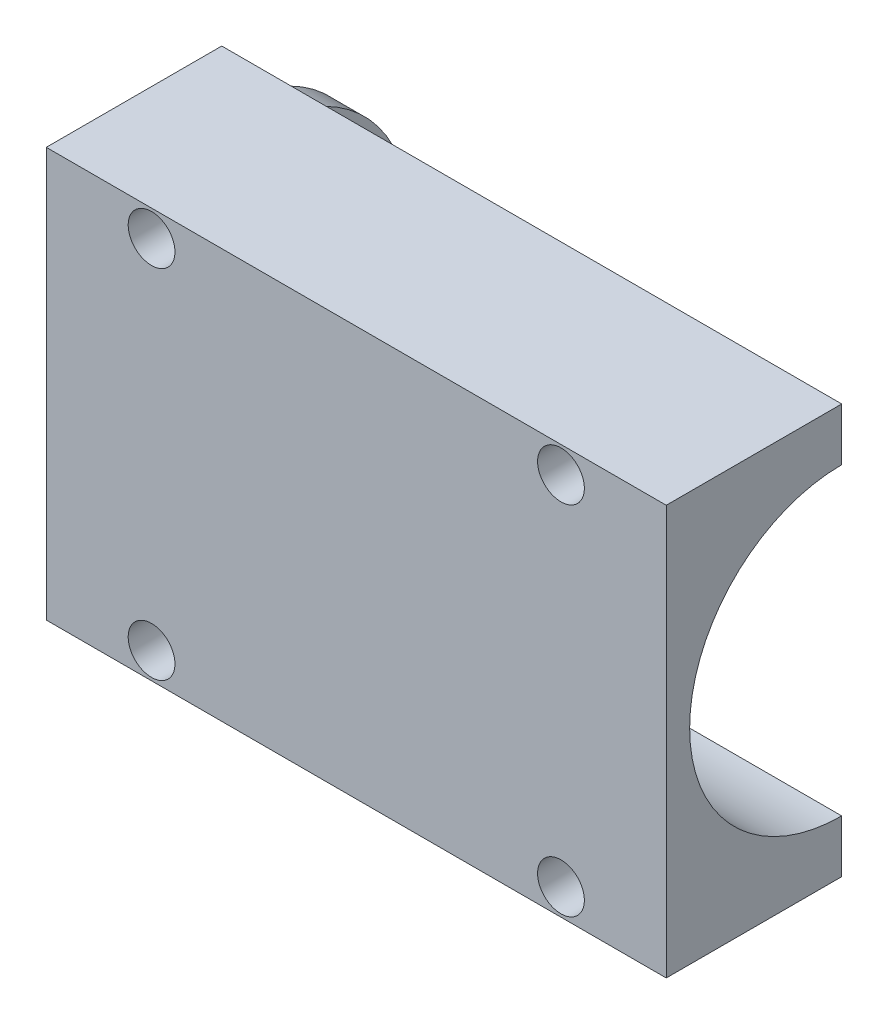
SolidWorks part; units mm, degrees
ref_plane "Front Plane" through (0, 0, 0) normal (0, 0, 1) x (1, 0, 0)
ref_plane "Top Plane" through (0, 0, 0) normal (0, 1, 0) x (1, 0, 0)
ref_plane "Right Plane" through (0, 0, 0) normal (1, 0, 0) x (0, 0, -1)
sketch "Sketch1" plane through (0, 0, 0) normal (0, 0, 1) x (1, 0, 0)
  line L1 (-26.5, -17.5) -> (26.5, -17.5)
  line L2 (-26.5, -17.5) -> (-26.5, 17.5)
  line L3 (-26.5, 17.5) -> (26.5, 17.5)
  line L4 (26.5, -17.5) -> (26.5, 17.5)
  line L5 (-26.5, -17.5) -> (26.5, 17.5) construction
  line L6 (-26.5, 17.5) -> (26.5, -17.5) construction
  point P0 (0, 0)
  point P5 (0, 0)
  dimension "D1" = 53
  dimension "D2" = 35
extrude "Boss-Extrude1" add sketch "Sketch1" along normal blind 15
sketch "Sketch2" plane through (0, 0, 0) normal (1, 0, 0) x (0, 0, -1)
  line L0 (0, -17.5) -> (0, 17.5) construction
  circle A0 centre (0, 0) radius 1.1
  dimension "D1" = 2.2
sketch "Sketch3" plane through (26.5, 0, 0) normal (1, 0, 0) x (0, 0, -1)
  line L0 (0, -17.5) -> (0, 17.5) construction
  circle A0 centre (0, 0) radius 13
  point P4 (0, 0)
  dimension "D1" = 26
extrude "Cut-Extrude1" cut sketch "Sketch3" against normal blind 50
sketch "Sketch6" plane through (-26.5, 0, 0) normal (-1, 0, 0) x (0, 0, 1)
  line L0 (0, 17.5) -> (0, -17.5) construction
  circle A0 centre (0, 0) radius 13
  dimension "D1" = 26
extrude "Boss-Extrude4" add sketch "Sketch6" against normal up to vertex
sketch "Sketch7" plane through (-26.5, 0, 0) normal (-1, 0, 0) x (0, 0, 1)
  circle A0 centre (0, 0) radius 4.5
  point P2 (0, 0)
  dimension "D1" = 9
extrude "Cut-Extrude2" cut sketch "Sketch7" against normal through all
sketch "Sketch8" plane through (0, 0, 0) normal (0, 0, -1) x (-1, 0, 0)
  circle A0 centre (0.8134, -0.9192) radius 0.1236
sketch "Sketch10" plane through (0, 0, 0) normal (0, 0, -1) x (-1, 0, 0)
  line L0 (-17.5, 15.25) -> (-17.5, -15.25) construction
  line L1 (-17.5, -15.25) -> (17.5, -15.25) construction
  line L2 (17.5, -15.25) -> (17.5, 15.25) construction
  line L3 (17.5, 15.25) -> (-17.5, 15.25) construction
  line L4 (-17.5, 15.25) -> (17.5, -15.25) construction
  circle A0 centre (-17.5, 15.25) radius 2
  circle A1 centre (17.5, 15.25) radius 2
  circle A2 centre (17.5, -15.25) radius 2
  circle A3 centre (-17.5, -15.25) radius 2
  point P8 (0, 0)
  dimension "D3" = 4
  dimension "D4" = 4
  dimension "D5" = 4
  dimension "D6" = 4
  dimension "D1" = 30.5
  dimension "D2" = 35
extrude "Cut-Extrude3" cut sketch "Sketch10" against normal through all
sketch "Sketch12" plane through (-26.5, 0, 0) normal (-1, 0, 0) x (0, 0, 1)
  line L0 (15, 17.5) -> (0, 17.5) construction
  line L1 (15, -17.5) -> (0, -17.5) construction
  circle A0 centre (0, 17.2) radius 0.1278
  circle A2 centre (0, -17.2) radius 0.1287
  dimension "D1" = 0.3
  dimension "D2" = 0.3
sketch "Sketch13" plane through (-23.5, 0, 0) normal (1, 0, 0) x (0, 0, -1)
  circle A0 centre (0, -1.4245) radius 0.131
  circle A1 centre (0, -3.0641) radius 0.1302
sketch "Sketch16" plane through (-23.5, 0, 0) normal (1, 0, 0) x (0, 0, -1)
  circle A0 centre (0, -1.4456) radius 0.1476
  circle A1 centre (0, -3.0683) radius 0.15
  dimension "D1" = 0.2952
  dimension "D2" = 0.3
sketch "Sketch17" plane through (-23.5, 0, 0) normal (1, 0, 0) x (0, 0, -1)
  line L0 (0, 8.5) -> (0, -8.5) construction
  circle A3 centre (0, -8.5) radius 1.75
  circle A4 centre (0, 8.5) radius 1.75
  point P4 (0, 0)
  dimension "D1" = 17
  dimension "D2" = 3.5
  dimension "D3" = 3.5
extrude "Cut-Extrude5" cut sketch "Sketch17" against normal through all
